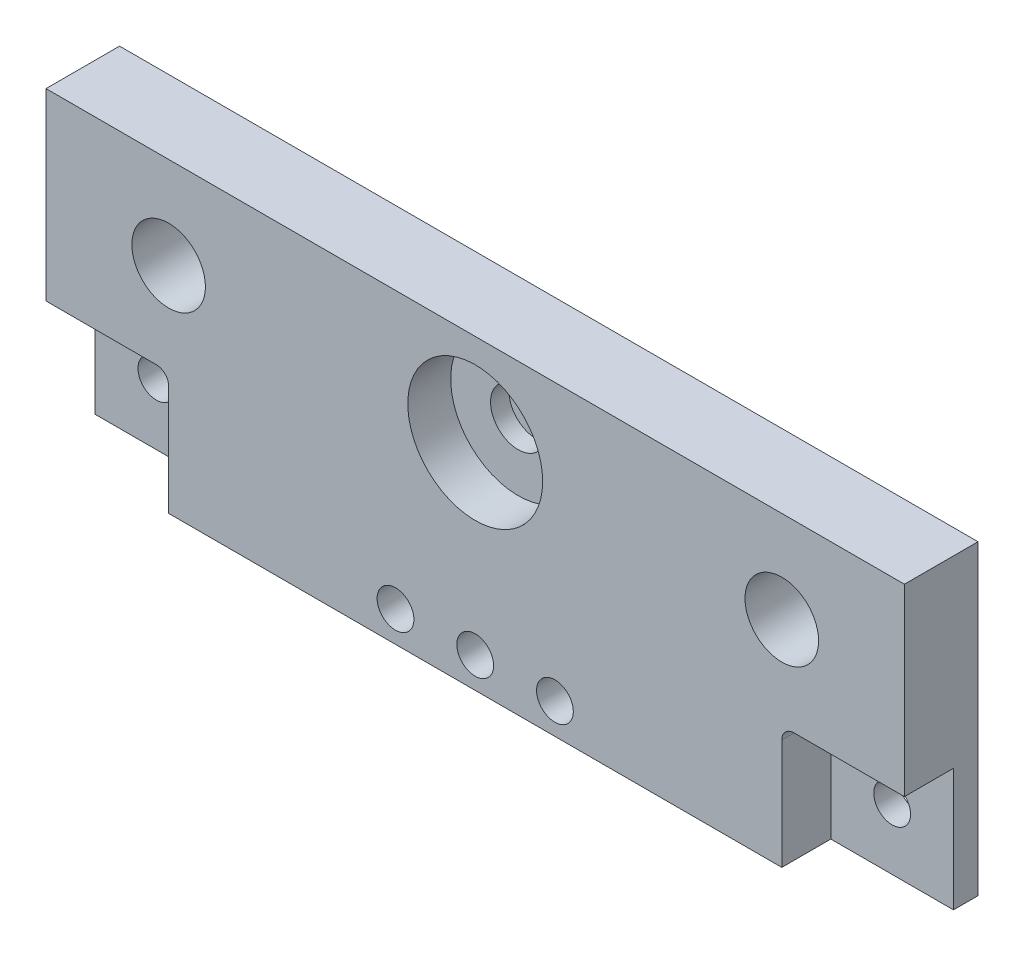
SolidWorks part; units mm, degrees
ref_plane "Plan de face" through (0, 0, 0) normal (0, 0, 1) x (1, 0, 0)
ref_plane "Plan de dessus" through (0, 0, 0) normal (0, 1, 0) x (1, 0, 0)
ref_plane "Plan de droite" through (0, 0, 0) normal (1, 0, 0) x (0, 0, -1)
sketch "Esquisse1" plane through (0, 0, 0) normal (0, 0, 1) x (1, 0, 0)
  line L0 (9.9563, -13.0813) -> (9.9563, -43.0813) construction
  line L1 (-60.0437, -13.0813) -> (79.9563, -13.0813)
  line L2 (-60.0437, -13.0813) -> (-60.0437, -43.0813)
  line L3 (-60.0437, -43.0813) -> (79.9563, -43.0813)
  line L4 (79.9563, -13.0813) -> (79.9563, -43.0813)
  line L5 (-60.0437, -28.0813) -> (79.9563, -28.0813) construction
  circle A0 centre (9.9563, -28.0813) radius 11
  circle A1 centre (-40.0437, -28.0813) radius 6
  circle A2 centre (59.9563, -28.0813) radius 6
  dimension "D3" = 22
  dimension "D4" = 12
  dimension "D5" = 12
  dimension "D1" = 30
  dimension "D2" = 140
  dimension "D6" = 100
  dimension "D7" = 50
extrude "Extrusion1" add sketch "Esquisse1" along normal blind 8
sketch "Esquisse2" plane through (0, 0, 0) normal (0, 0, -1) x (-1, 0, 0)
  line L1 (-79.9563, -13.0813) -> (60.0437, -13.0813)
  line L2 (-79.9563, -13.0813) -> (-79.9563, -63.0813)
  line L3 (-79.9563, -63.0813) -> (60.0437, -63.0813)
  line L4 (60.0437, -13.0813) -> (60.0437, -63.0813)
  dimension "D1" = 140
  dimension "D2" = 50
extrude "Boss.-Extru.1" add sketch "Esquisse2" along normal blind 4
sketch "Esquisse3" plane through (0, 0, -4) normal (0, 0, -1) x (-1, 0, 0)
  line L0 (-79.9563, -53.0813) -> (60.0437, -53.0813) construction
  line L1 (-79.9563, -13.0813) -> (-79.9563, -63.0813) construction
  line L2 (60.0437, -63.0813) -> (60.0437, -13.0813) construction
  line L3 (-79.9563, -63.0813) -> (60.0437, -63.0813) construction
  circle A0 centre (-69.9563, -53.0813) radius 3
  circle A1 centre (50.0437, -53.0813) radius 3
  dimension "D2" = 6
  dimension "D3" = 6
  dimension "D5" = 10
  dimension "D1" = 10
  dimension "D4" = 10
extrude "Enlèv. mat.-Extru.1" cut sketch "Esquisse3" against normal through all
sketch "Esquisse4" plane through (0, 0, 0) normal (0, 0, 1) x (1, 0, 0)
  circle A0 centre (9.9563, -28.0813) radius 11
extrude "Enlèv. mat.-Extru.2" cut sketch "Esquisse4" against normal blind 2
sketch "Esquisse5" plane through (0, 0, 0) normal (0, 0, 1) x (1, 0, 0)
  line L0 (-60.0437, -43.0813) -> (79.9563, -43.0813) construction
  line L1 (-40.0437, -43.0813) -> (59.9563, -43.0813)
  line L2 (-40.0437, -43.0813) -> (-40.0437, -63.0813)
  line L3 (-40.0437, -63.0813) -> (59.9563, -63.0813)
  line L4 (59.9563, -43.0813) -> (59.9563, -63.0813)
  line L5 (79.9563, -63.0813) -> (-60.0437, -63.0813) construction
  line L6 (-60.0437, -63.0813) -> (-60.0437, -43.0813) construction
  line L7 (79.9563, -43.0813) -> (79.9563, -63.0813) construction
  dimension "D1" = 20
  dimension "D2" = 20
extrude "Boss.-Extru.2" add sketch "Esquisse5" along normal blind 8
sketch "Esquisse6" plane through (0, 0, 8) normal (0, 0, 1) x (1, 0, 0)
  line L0 (-40.0437, -58.0813) -> (59.9563, -58.0813) construction
  line L1 (-40.0437, -43.0813) -> (-40.0437, -63.0813) construction
  line L2 (59.9563, -63.0813) -> (59.9563, -43.0813) construction
  line L3 (9.9563, -13.0813) -> (9.9563, -63.0813) construction
  line L4 (-40.0437, -63.0813) -> (59.9563, -63.0813) construction
  line L5 (79.9563, -13.0813) -> (-60.0437, -13.0813) construction
  circle A0 centre (22.9563, -58.0813) radius 3
  circle A1 centre (-3.0437, -58.0813) radius 3
  dimension "D2" = 6
  dimension "D3" = 6
  dimension "D1" = 5
  dimension "D4" = 26
  dimension "D5" = 13
extrude "Enlèv. mat.-Extru.3" cut sketch "Esquisse6" against normal blind 8
sketch "Esquisse8" plane through (0, 0, 0) normal (0, 0, 1) x (1, 0, 0)
  circle A0 centre (-40.0437, -28.0813) radius 6
  circle A1 centre (59.9563, -28.0813) radius 6
extrude "Enlèv. mat.-Extru.4" cut sketch "Esquisse8" against normal blind 2
sketch "Esquisse9" plane through (0, 0, -2) normal (0, 0, 1) x (1, 0, 0)
  circle A0 centre (9.9563, -28.0813) radius 11
  circle A1 centre (9.9563, -28.0813) radius 4.5
  dimension "D1" = 9
extrude "Boss.-Extru.3" add sketch "Esquisse9" along normal blind 3
sketch "Esquisse10" plane through (0, 0, 8) normal (0, 0, 1) x (1, 0, 0)
  line L0 (-60.0437, -63.0813) -> (-60.0437, -43.0813) construction
  line L1 (-40.0437, -63.0813) -> (59.9563, -63.0813) construction
  circle A0 centre (9.9563, -58.0813) radius 3
  dimension "D2" = 6
  dimension "D1" = 70
  dimension "D3" = 5
extrude "Enlèv. mat.-Extru.5" cut sketch "Esquisse10" against normal through all
fillet "Congé1" radius 2 1 edges at (-40.0437, -43.0813, 4)
fillet "Congé2" radius 2 1 edges at (59.9563, -43.0813, 4)
